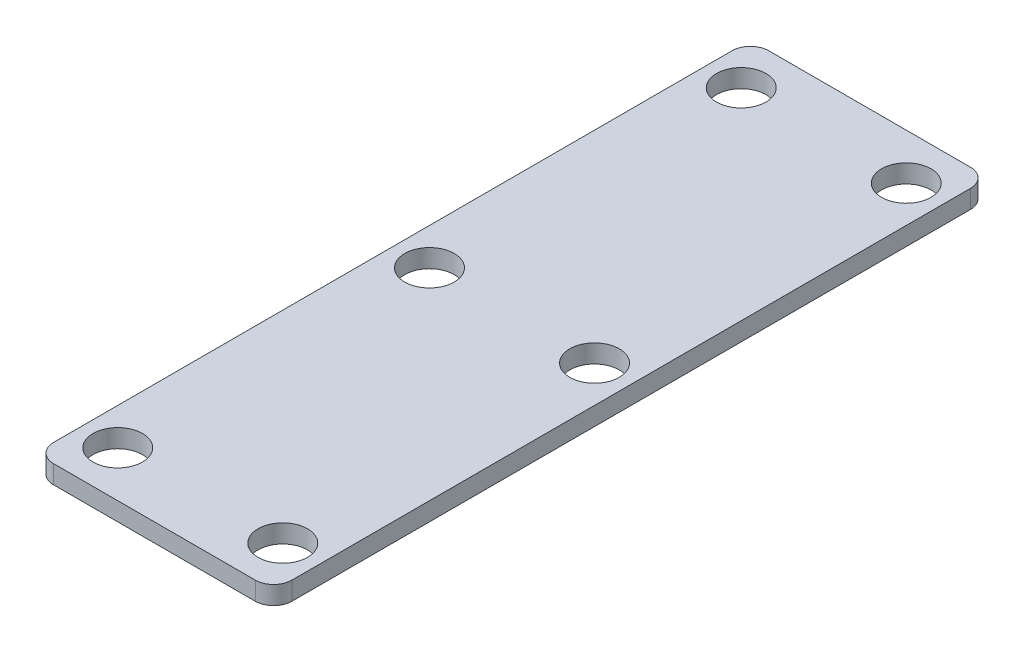
SolidWorks part; units mm, degrees
material "1060 Alloy"
ref_plane "Front Plane" through (0, 0, 0) normal (0, 0, 1) x (1, 0, 0)
ref_plane "Top Plane" through (0, 0, 0) normal (0, 1, 0) x (1, 0, 0)
ref_plane "Right Plane" through (0, 0, 0) normal (1, 0, 0) x (0, 0, -1)
sketch "Sketch1" plane through (0, 0, 0) normal (0, 1, 0) x (1, 0, 0)
  line L1 (-6.5, -19.5) -> (6.5, -19.5)
  line L2 (-6.5, -19.5) -> (-6.5, 19.5)
  line L3 (-6.5, 19.5) -> (6.5, 19.5)
  line L4 (6.5, -19.5) -> (6.5, 19.5)
  line L5 (-6.5, -19.5) -> (6.5, 19.5) construction
  line L6 (-6.5, 19.5) -> (6.5, -19.5) construction
  point P0 (0, 0)
  dimension "D1" = 39
  dimension "D2" = 13
extrude "Boss-Extrude1" add sketch "Sketch1" along normal blind 1
sketch "Sketch2" plane through (0, 1, 0) normal (0, 1, 0) x (1, 0, 0)
  line L0 (6.5, 0) -> (4.5, 0)
  line L1 (6.5, -19.5) -> (6.5, 19.5) construction
  line L2 (4.5, 0) -> (4.5, 17)
  line L3 (4.5, 0) -> (4.5, -17)
  line L4 (-6.5, 0) -> (-4.5, 0)
  line L5 (-6.5, 19.5) -> (-6.5, -19.5) construction
  line L6 (-4.5, 0) -> (-4.5, 17)
  line L7 (-4.5, 0) -> (-4.5, -17)
  circle A0 centre (4.5, 17) radius 1.35
  circle A1 centre (-4.5, 17) radius 1.35
  circle A2 centre (-4.5, 0) radius 1.35
  circle A3 centre (-4.5, -17) radius 1.35
  circle A4 centre (4.5, -17) radius 1.35
  circle A5 centre (4.5, 0) radius 1.35
  dimension "D5" = 2.7
  dimension "D6" = 2.7
  dimension "D7" = 2.7
  dimension "D8" = 2.7
  dimension "D9" = 2.7
  dimension "D10" = 2.7
  dimension "D1" = 17
  dimension "D2" = 17
  dimension "D3" = 17
  dimension "D4" = 17
  dimension "D11" = 2
  dimension "D12" = 2
extrude "Cut-Extrude1" cut sketch "Sketch2" against normal through all
fillet "Fillet1" radius 1 4 edges at (-6.5, 0.5, 19.5) (6.5, 0.5, 19.5) (6.5, 0.5, -19.5) (-6.5, 0.5, -19.5)
